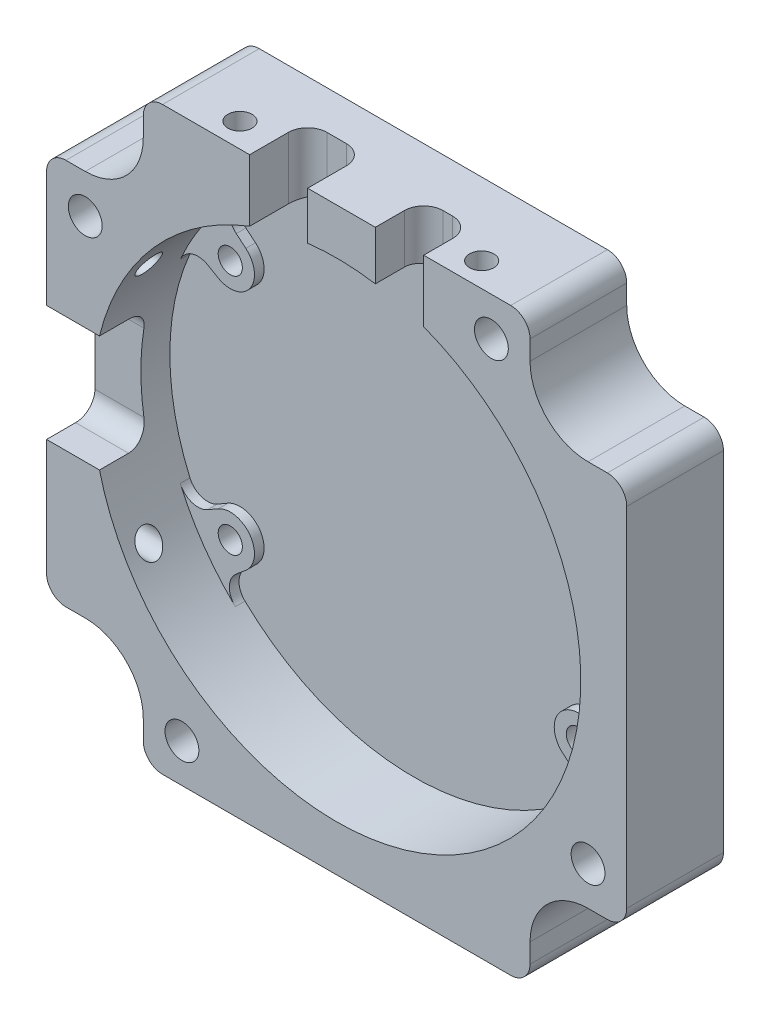
SolidWorks part; units mm, degrees
material "3.3326 (EN-AW 5051A)"
ref_plane "前视基准面" through (0, 0, 0) normal (0, 0, 1) x (1, 0, 0)
ref_plane "上视基准面" through (0, 0, 0) normal (0, 1, 0) x (1, 0, 0)
ref_plane "右视基准面" through (0, 0, 0) normal (1, 0, 0) x (0, 0, -1)
other "Configuration Table"
sketch "草图1" plane through (0, 0, 0) normal (0, 0, 1) x (1, 0, 0)
  line L1 (0, 0) -> (60, 0)
  line L2 (0, 0) -> (0, -60)
  line L3 (0, -60) -> (60, -60)
  line L4 (60, 0) -> (60, -60)
  dimension "D1" = 60
  dimension "D2" = 60
extrude "凸台-拉伸1" add sketch "草图1" along normal blind 10
sketch "草图2" plane through (0, 0, 10) normal (0, 0, 1) x (1, 0, 0)
  circle A0 centre (30, -30) radius 25.25
  dimension "D1" = 50.5
extrude "切除-拉伸1" cut sketch "草图2" against normal blind 8
sketch "草图4" plane through (0, 0, 0) normal (0, 0, -1) x (-1, 0, 0)
  line L0 (-10, 0) -> (-10, -10)
  line L1 (-60, 0) -> (-50, 0)
  line L2 (-60, 0) -> (-60, -10)
  line L3 (-60, -10) -> (-50, -10)
  line L4 (-50, 0) -> (-50, -10)
  line L5 (-10, 0) -> (0, 0)
  line L6 (0, 0) -> (0, -10)
  line L7 (-10, -10) -> (0, -10)
  line L8 (-10, -50) -> (-10, -60)
  line L9 (-10, -50) -> (0, -50)
  line L10 (0, -50) -> (0, -60)
  line L11 (-10, -60) -> (0, -60)
  line L12 (-60, -50) -> (-60, -60)
  line L13 (-60, -50) -> (-50, -50)
  line L14 (-50, -50) -> (-50, -60)
  line L15 (-60, -60) -> (-50, -60)
  dimension "D1" = 10
  dimension "D2" = 10
  dimension "D3" = 2
  dimension "D4" = 2
extrude "切除-拉伸3" cut sketch "草图4" against normal through all
fillet "圆角1" radius 6 4 edges at (10, -50, 5) (50, -50, 5) (10, -10, 5) (50, -10, 5)
fillet "圆角2" radius 2 8 edges at (10, -60, 5) (0, -50, 5) (0, -10, 5) (10, 0, 5) (50, 0, 5) (60, -10, 5) (60, -50, 5) (50, -60, 5)
sketch "草图5" plane through (0, 0, 0) normal (0, 0, -1) x (-1, 0, 0)
  line L0 (0, -12) -> (0, -48) construction
  line L1 (-4, -10) -> (-2, -10) construction
  line L3 (-48, 0) -> (-12, 0) construction
  line L4 (-50, -4) -> (-50, -2) construction
  line L5 (-12, -60) -> (-48, -60) construction
  line L6 (-10, -56) -> (-10, -58) construction
  line L7 (-56, -50) -> (-58, -50) construction
  line L8 (-60, -48) -> (-60, -12) construction
  circle A10 centre (-4, -14) radius 1.75
  circle A11 centre (-14, -56) radius 1.75
  circle A12 centre (-56, -46) radius 1.75
  circle A13 centre (-46, -4) radius 1.75
  dimension "D1" = 4
  dimension "D2" = 4
  dimension "D3" = 4
  dimension "D4" = 4
  dimension "D5" = 3.5
  dimension "D10" = 3.5
  dimension "D11" = 3.5
  dimension "D12" = 3.5
  dimension "D6" = 4
  dimension "D7" = 4
  dimension "D8" = 4
  dimension "D9" = 4
extrude "切除-拉伸4" cut sketch "草图5" against normal through all
sketch "草图15" plane through (0, 0, 2) normal (0, 0, 1) x (1, 0, 0)
  line L1 (12, -17.5) -> (48, -17.5) construction
  line L2 (12, -17.5) -> (12, -42.5) construction
  line L3 (12, -42.5) -> (48, -42.5) construction
  line L4 (48, -17.5) -> (48, -42.5) construction
  line L5 (30, -30) -> (30, -4.75) construction
  line L7 (30, -30) -> (55.25, -30) construction
  line L14 (46.393, -15.5849) -> (49.0139, -13.3857)
  line L15 (49.25, -19.6651) -> (52.1967, -17.9638)
  line L16 (13.607, -15.5849) -> (10.9861, -13.3857)
  line L17 (10.75, -19.6651) -> (7.8033, -17.9638)
  line L18 (46.393, -44.4151) -> (49.0139, -46.6143)
  line L19 (49.25, -40.3349) -> (52.1967, -42.0362)
  line L20 (10.75, -40.3349) -> (7.8033, -42.0362)
  line L21 (13.607, -44.4151) -> (10.9861, -46.6143)
  circle A0 centre (30, -30) radius 25.25 construction
  circle A3 centre (30, -30) radius 25.25 construction
  arc A11 (46.393, -15.5849) -> (49.25, -19.6651) centre (48, -17.5) ccw
  arc A12 (52.1967, -17.9638) -> (49.0139, -13.3857) centre (30, -30) ccw
  arc A13 (7.8033, -17.9638) -> (10.9861, -13.3857) centre (30, -30) cw
  arc A14 (13.607, -15.5849) -> (10.75, -19.6651) centre (12, -17.5) cw
  arc A15 (52.1967, -42.0362) -> (49.0139, -46.6143) centre (30, -30) cw
  arc A16 (46.393, -44.4151) -> (49.25, -40.3349) centre (48, -42.5) cw
  arc A17 (13.607, -44.4151) -> (10.75, -40.3349) centre (12, -42.5) ccw
  arc A18 (7.8033, -42.0362) -> (10.9861, -46.6143) centre (30, -30) ccw
  dimension "D3" = 5
  dimension "D1" = 25
  dimension "D2" = 36
extrude "凸台-拉伸2" add sketch "草图15" along normal blind 1
fillet "圆角5" radius 2 8 edges at (10.9861, -13.3857, 2.5) (7.8033, -17.9638, 2.5) (7.8033, -42.0362, 2.5) (10.9861, -46.6143, 2.5) (49.0139, -46.6143, 2.5) (52.1967, -42.0362, 2.5) (52.1967, -17.9638, 2.5) (49.0139, -13.3857, 2.5)
hole_wizard "M3 螺纹孔2" positions "草图20" profile "草图19" tap size "M3" standard "GB"
sketch "草图20" plane through (0, 0, 3) normal (0, 0, 1) x (1, 0, 0)
  point P0 (12, -17.5)
  point P3 (12, -42.5)
  point P6 (48, -17.5)
  point P9 (48, -42.5)
sketch "草图19" plane through (12, -17.5, 3) normal (1, 0, 0) x (0, -1, 0)
  line L0 (0, 0) -> (0, 8.2511)
  line L1 (0, 8.2511) -> (1.25, 7.5)
  line L2 (1.25, 7.5) -> (1.25, 0)
  line L5 (1.25, 0) -> (0, 0)
  line L10 (0, 8.2511) -> (-1.25, 7.5) construction
  line L11 (0, -6.35) -> (0, 107.95) construction
  dimension "螺纹孔钻头直径" = 2.5
  dimension "螺纹孔钻头深度" = 7.5
  dimension "导头角度" = 118
cosmetic thread "孔螺蚊线5" parameters "D1"=6, "D2"=3
cosmetic thread "孔螺蚊线6" parameters "D1"=6, "D2"=3
cosmetic thread "孔螺蚊线7" parameters "D1"=6, "D2"=3
cosmetic thread "孔螺蚊线8" parameters "D1"=6, "D2"=3
sketch "草图21" plane through (0, 0, 0) normal (0, 1, 0) x (1, 0, 0)
  line L0 (48, -10) -> (12, -10) construction
  line L1 (34, -10) -> (39, -10)
  line L2 (34, -10) -> (34, -5)
  line L3 (34, -5) -> (39, -5)
  line L4 (39, -10) -> (39, -5)
  line L5 (60, 0) -> (60, -10) construction
  line L6 (48, -10) -> (48, 0) construction
  line L8 (21, -10) -> (27, -10)
  line L9 (21, -10) -> (21, -4)
  line L10 (21, -4) -> (27, -4)
  line L11 (27, -10) -> (27, -4)
  circle A0 centre (17.5, -7.5) radius 1.25
  circle A1 centre (42.5, -7.5) radius 1.25
  dimension "D3" = 2.5
  dimension "D4" = 2.5
  dimension "D1" = 5
  dimension "D2" = 5
  dimension "D5" = 2.5
  dimension "D6" = 25
  dimension "D7" = 17.5
  dimension "D8" = 2.5
  dimension "D9" = 9
  dimension "D10" = 6
  dimension "D11" = 6
  dimension "D12" = 7
extrude "切除-拉伸9" cut sketch "草图21" against normal blind 10
sketch "草图23" plane through (0, 0, 0) normal (-1, 0, 0) x (0, 0, 1)
  line L0 (10, -12) -> (10, -48) construction
  line L1 (10, -24) -> (5, -24)
  line L2 (10, -24) -> (10, -36)
  line L3 (10, -36) -> (5, -36)
  line L4 (5, -24) -> (5, -36)
  line L5 (10, -60) -> (0, -60) construction
  circle A0 centre (7.5, -17.5) radius 1.25
  circle A1 centre (7.5, -42.5) radius 1.25
  dimension "D8" = 2.5
  dimension "D9" = 2.5
  dimension "D1" = 5
  dimension "D2" = 12
  dimension "D3" = 24
  dimension "D4" = 25
  dimension "D5" = 17.5
  dimension "D6" = 2.5
  dimension "D7" = 2.5
extrude "切除-拉伸10" cut sketch "草图23" against normal blind 10
sketch "草图25" plane through (0, 0, 0) normal (0, 0, -1) x (-1, 0, 0)
  circle A0 centre (-56, -46) radius 1.75 construction
  circle A1 centre (-14, -56) radius 1.75 construction
  circle A2 centre (-4, -14) radius 1.75 construction
  circle A3 centre (-46, -4) radius 1.75 construction
  circle A20 centre (-56, -46) radius 1.75 construction
  circle A21 centre (-14, -56) radius 1.75 construction
  circle A22 centre (-4, -14) radius 1.75 construction
  circle A23 centre (-46, -4) radius 1.75 construction
  circle A24 centre (-4, -14) radius 2.75
  circle A25 centre (-46, -4) radius 2.75
  circle A26 centre (-56, -46) radius 2.75
  circle A27 centre (-14, -56) radius 2.75
  dimension "D1" = 1
extrude "切除-拉伸11" cut sketch "草图25" against normal blind 3
fillet "圆角6" radius 2 6 edges at (2.7366, -36, 5) (2.7366, -24, 5) (21, -3.2042, 4) (27, -2.4644, 4) (34, -2.5344, 5) (39, -3.2042, 5)
